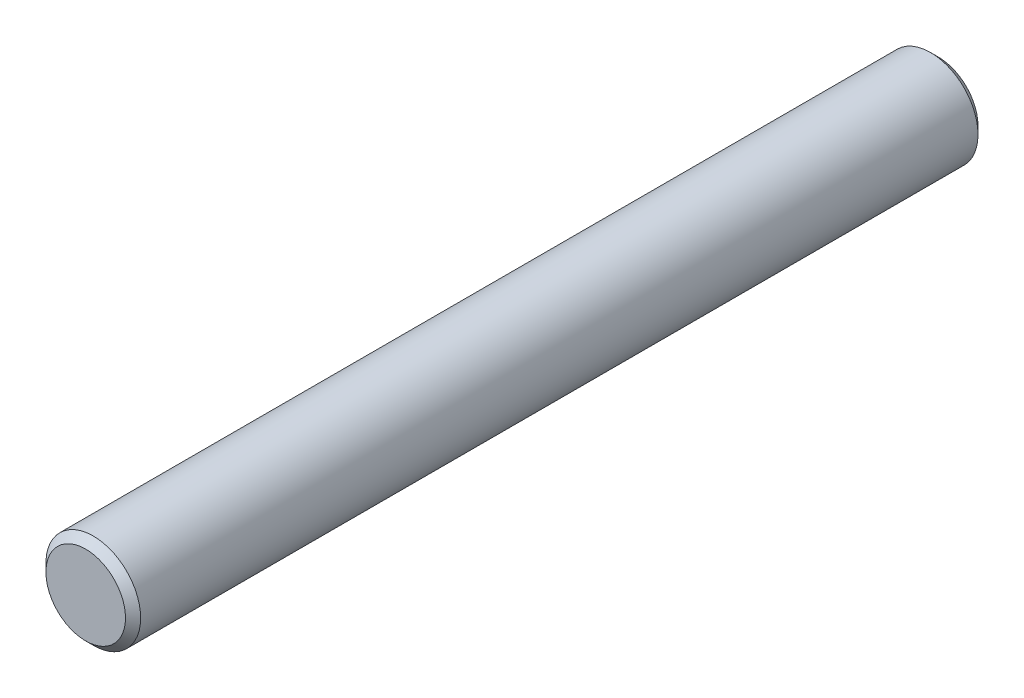
SolidWorks part; units mm, degrees
material "Plain Carbon Steel"
ref_plane "Front Plane" through (0, 0, 0) normal (0, 0, 1) x (1, 0, 0)
ref_plane "Top Plane" through (0, 0, 0) normal (0, 1, 0) x (1, 0, 0)
ref_plane "Right Plane" through (0, 0, 0) normal (1, 0, 0) x (0, 0, -1)
sketch "Sketch1" plane through (0, 0, 0) normal (0, 0, 1) x (1, 0, 0)
  circle A0 centre (0, 0) radius 2.5
  dimension "D1" = 5
extrude "Boss-Extrude1" add sketch "Sketch1" along normal blind 45
chamfer "Chamfer1" distance 0.4 angle 45 2 edges at (2.5, 0, 0) (2.5, 0, 45)
